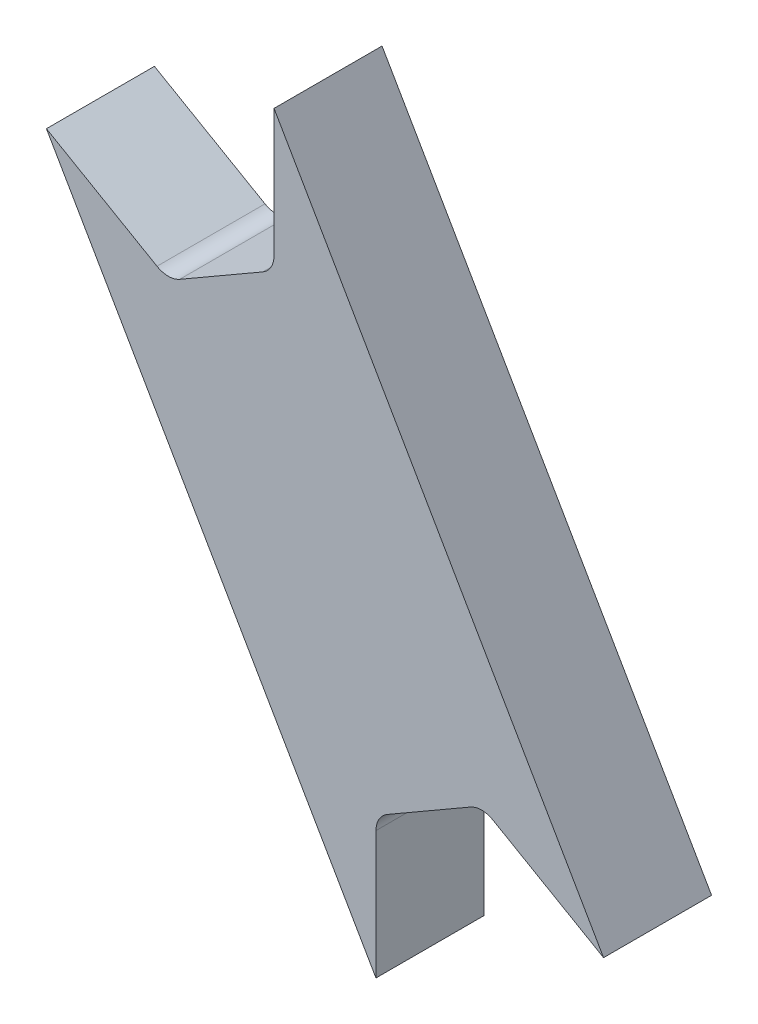
SolidWorks part; units mm, degrees
material "PVC Rigid"
ref_plane "Front Plane" through (0, 0, 0) normal (0, 0, 1) x (1, 0, 0)
ref_plane "Top Plane" through (0, 0, 0) normal (0, 1, 0) x (1, 0, 0)
ref_plane "Right Plane" through (0, 0, 0) normal (1, 0, 0) x (0, 0, -1)
sketch "Sketch3" plane through (0, 0, 0) normal (0, 0, 1) x (1, 0, 0)
  line L0 (-6.5, -3.7528) -> (0, -7.5056) construction
  line L1 (6.5, 3.7528) -> (6.5, -3.7528) construction
  line L2 (1.0795, -7.5056) -> (5.9602, -4.6877) construction
  line L3 (26.127, -29.8022) -> (19.627, -26.0495)
  line L4 (6.5, -3.7528) -> (0, -7.5056) construction
  line L5 (-6.627, -3.9727) -> (-0.127, -7.7255)
  line L6 (1.2065, -7.7255) -> (6.0872, -4.9076)
  line L7 (6.754, 3.7528) -> (6.754, -3.7528)
  line L8 (-6.627, -3.9727) -> (12.746, -37.5278)
  line L9 (3.0595, -20.7503) -> (16.4405, -13.0247) construction
  line L10 (26.127, -29.8022) -> (6.754, 3.7528)
  line L11 (13.4128, -28.8674) -> (18.2935, -26.0495)
  line L12 (12.746, -37.5278) -> (12.746, -30.0222)
  arc A0 (0, -7.5056) -> (1.0795, -7.5056) centre (0.5398, -6.5707) ccw construction
  arc A1 (5.9602, -4.6877) -> (6.5, -3.7528) centre (5.4205, -3.7528) ccw construction
  arc A2 (-0.127, -7.7255) -> (1.2065, -7.7255) centre (0.5398, -6.5707) ccw
  arc A3 (6.0872, -4.9076) -> (6.754, -3.7528) centre (5.4205, -3.7528) ccw
  arc A4 (18.2935, -26.0495) -> (19.627, -26.0495) centre (18.9602, -27.2043) cw
  arc A5 (12.746, -30.0222) -> (13.4128, -28.8674) centre (14.0795, -30.0222) cw
  circle A6 centre (9.75, -16.8875) radius 3.175 construction
  point P12 (-1.7776, -16.4244)
  point P14 (9.75, -16.8875)
  dimension "D1" = 0.7937
  dimension "D3" = 6.35
  dimension "D2" = 0.254
extrude "Boss-Extrude1" add sketch "Sketch3" against normal blind 6.35
